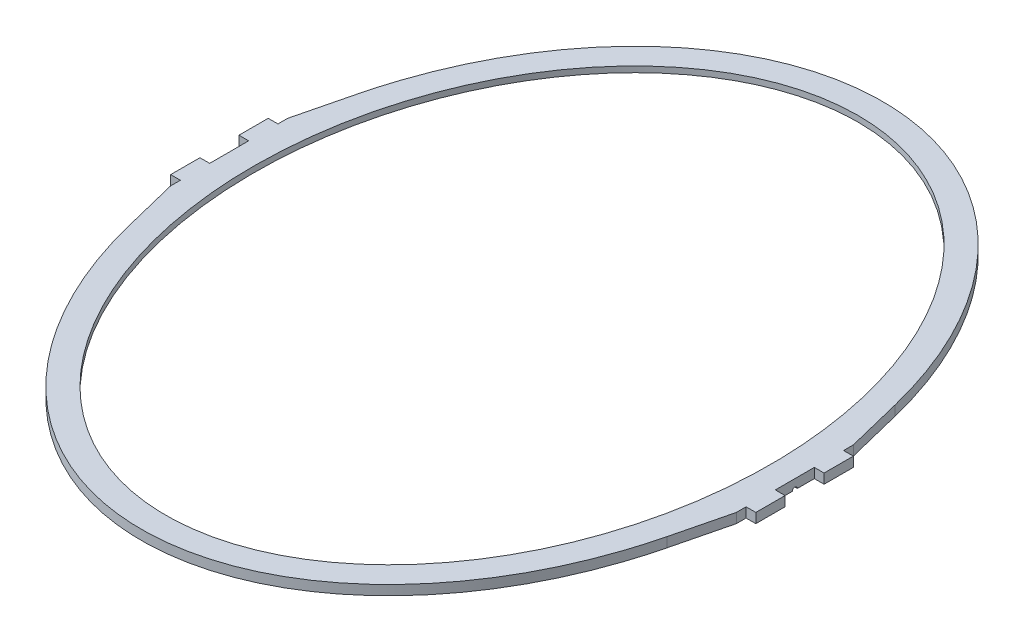
SolidWorks part; units mm, degrees
ref_plane "Front Plane" through (0, 0, 0) normal (0, 0, 1) x (1, 0, 0)
ref_plane "Top Plane" through (0, 0, 0) normal (0, 1, 0) x (1, 0, 0)
ref_plane "Right Plane" through (0, 0, 0) normal (1, 0, 0) x (0, 0, -1)
sketch "Sketch1" plane through (0, 0, 0) normal (0, 1, 0) x (1, 0, 0)
  line L0 (0, 520.2694) -> (0, -520.3963) construction
  line L1 (-478.2136, 0) -> (435.079, 0) construction
  line L2 (-270, 0) -> (-270, 60) construction
  line L3 (-270, 60) -> (-290, 60) construction
  line L4 (-290, 60) -> (-290, -60) construction
  line L5 (-290, 60) -> (-275.8919, 117.0811)
  line L6 (290, -60) -> (275.8919, -117.0811)
  line L7 (-290, -60) -> (-275.8919, -117.0811)
  line L8 (290, 60) -> (275.8919, 117.0811)
  line L9 (290, 60) -> (290, -60) construction
  line L10 (290, 50) -> (300, 50)
  line L11 (300, 50) -> (300, 20)
  line L12 (300, 20) -> (290, 20)
  line L13 (290, 50) -> (290, 60)
  line L14 (290, 20) -> (290, -20)
  line L15 (290, -50) -> (290, -60)
  line L16 (300, -20) -> (290, -20)
  line L17 (300, -50) -> (300, -20)
  line L18 (290, -50) -> (300, -50)
  line L19 (-290, 60) -> (-290, -60) construction
  line L20 (-290, -50) -> (-300, -50)
  line L21 (-300, -50) -> (-300, -20)
  line L22 (-300, -20) -> (-290, -20)
  line L23 (-290, -50) -> (-290, -60)
  line L24 (-290, 20) -> (-290, -20)
  line L25 (-290, 50) -> (-290, 60)
  line L26 (-300, 20) -> (-290, 20)
  line L27 (-300, 50) -> (-300, 20)
  line L28 (-290, 50) -> (-300, 50)
  ellipse E0 centre (0, 0) end of major axis (0, 355) minor radius 265
  ellipse E1 centre (0, 0) end of major axis (0, 380) minor radius 290 construction
  ellipse E2 centre (0, 0) end of major axis (0, 380) minor radius 290 (-275.8919, 117.0811) -> (275.8919, 117.0811) cw
  ellipse E4 centre (0, 0) end of major axis (0, -380) minor radius 290 (-275.8919, -117.0811) -> (275.8919, -117.0811) ccw
  point P27 (290, 0)
  point P32 (-290, 0)
  point P42 (290, 0)
  dimension "D1" = 530
  dimension "D2" = 710
  dimension "D3" = 580
  dimension "D4" = 760
  dimension "D5" = 20
  dimension "D6" = 30
  dimension "D7" = 60
  dimension "D8" = 10
  dimension "D9" = 10
extrude "Boss-Extrude1" add sketch "Sketch1" along normal blind 10
sketch "Sketch2" plane through (0, 0, 0) normal (0, -1, 0) x (1, 0, 0)
  line L0 (0, -520.2694) -> (0, 520.3963) construction
  ellipse E0 centre (0, 0) end of major axis (0, 355) minor radius 265
  ellipse E2 centre (0, 0) end of major axis (0, 365) minor radius 275
  dimension "D1" = 10
  dimension "D2" = 10
extrude "Cut-Extrude1" cut sketch "Sketch2" against normal blind 4
sketch "Sketch4" plane through (-290, 0, 0) normal (-1, 0, 0) x (0, 0, 1)
  line L0 (-2.5, 0) -> (2.5, 0)
  arc A0 (2.5, 0) -> (-2.5, 0) centre (0, 0) ccw
  dimension "D1" = 5
extrude "Cut-Extrude4" cut sketch "Sketch4" against normal blind 10 from surface at 0 starting at face at (-290, 5, 0)
sketch "Sketch5" plane through (290, 0, 0) normal (1, 0, 0) x (0, 0, -1)
  line L1 (-2.5, 0) -> (2.5, 0)
  line L2 (-20, 0) -> (20, 0) construction
  arc A0 (2.5, 0) -> (-2.5, 0) centre (0, 0) ccw
  dimension "D1" = 5
extrude "Cut-Extrude5" cut sketch "Sketch5" against normal blind 10
